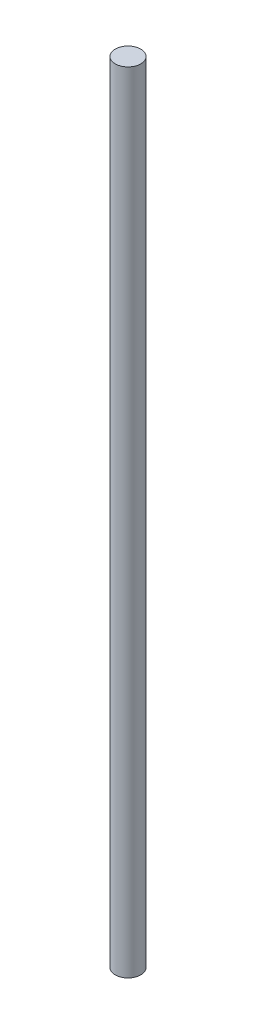
SolidWorks part; units mm, degrees
ref_plane "Plan de face" through (0, 0, 0) normal (0, 0, 1) x (1, 0, 0)
ref_plane "Plan de dessus" through (0, 0, 0) normal (0, 1, 0) x (1, 0, 0)
ref_plane "Plan de droite" through (0, 0, 0) normal (1, 0, 0) x (0, 0, -1)
sketch "Esquisse1" plane through (0, 0, 0) normal (0, 1, 0) x (1, 0, 0)
  circle A0 centre (0, 0) radius 1.5
  dimension "D1" = 3
extrude "Boss.-Extru.1" add sketch "Esquisse1" along normal blind 92.4
